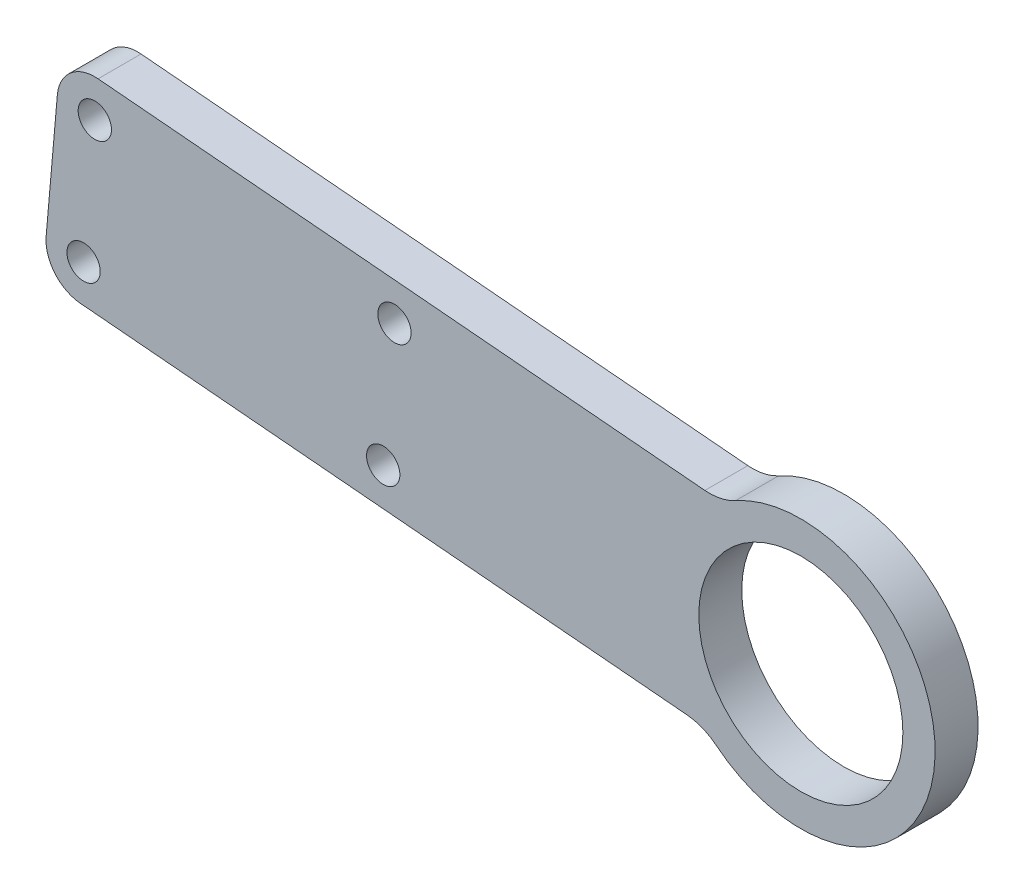
SolidWorks part; units mm, degrees
ref_plane "前视基准面" through (0, 0, 0) normal (0, 0, 1) x (1, 0, 0)
ref_plane "上视基准面" through (0, 0, 0) normal (0, 1, 0) x (1, 0, 0)
ref_plane "右视基准面" through (0, 0, 0) normal (1, 0, 0) x (0, 0, -1)
sketch "草图1" plane through (0, 0, 0) normal (0, 0, 1) x (1, 0, 0)
  line L0 (0, 0) -> (160, 0) construction
  line L1 (-8.9271, 3.2492) -> (-1.4962, 23.6654)
  line L2 (-1.4962, 23.6654) -> (160.828, 9.4638)
  line L3 (8.9271, -3.2492) -> (11.3716, 3.467)
  line L4 (11.3716, 3.467) -> (159.172, -9.4638)
  circle A0 centre (0, 0) radius 6
  arc A1 (-8.9271, 3.2492) -> (8.9271, -3.2492) centre (0, 0) ccw
  arc A2 (159.172, -9.4638) -> (160.828, 9.4638) centre (160, 0) ccw
  circle A3 centre (160, 0) radius 6
  dimension "D1" = 12
  dimension "D2" = 19
  dimension "D3" = 160
  dimension "D4" = 70
  dimension "D5" = 5
extrude "凸台-拉伸1" add sketch "草图1" along normal mid plane 4
sketch "草图2" plane through (0, 0, 2) normal (0, 0, 1) x (1, 0, 0)
  line L0 (8.9271, -3.2492) -> (11.3716, 3.467) construction
  line L1 (160.828, 9.4638) -> (-1.4962, 23.6654) construction
  line L2 (-1.4962, 23.6654) -> (-8.9271, 3.2492) construction
  line L3 (11.3716, 3.467) -> (159.172, -9.4638) construction
  circle A0 centre (0.8742, 19.9446) radius 1.55
  circle A1 centre (16.2206, 6.5562) radius 1.55
  circle A2 centre (11.9354, 3.2618) radius 0.6
  dimension "D1" = 3.5
  dimension "D2" = 3.5
  dimension "D3" = 3.5
  dimension "D4" = 3.5
  dimension "D5" = 3.1
  dimension "D6" = 1.2
extrude "切除-拉伸1" cut sketch "草图2" against normal through all
fillet "圆角1" radius 3.5 1 edges at (-1.4962, 23.6654, 0)
sketch "草图3" plane through (0, 0, 2) normal (0, 0, 1) x (1, 0, 0)
  line L0 (91.0944, 15.5648) -> (89.4384, -3.3629)
  line L1 (160.828, 9.4638) -> (1.1792, 23.4313) construction
  line L2 (12.5263, 3.366) -> (159.172, -9.4638) construction
  line L3 (89.4384, -3.3629) -> (159.172, -9.4638)
  line L4 (160.828, 9.4638) -> (91.0944, 15.5648)
  arc A0 (159.172, -9.4638) -> (160.828, 9.4638) centre (160, 0) ccw
  dimension "D1" = 70
extrude "切除-拉伸2" cut sketch "草图3" against normal through all flip side to cut
sketch "草图4" plane through (0, 0, 2) normal (0, 0, 1) x (1, 0, 0)
  line L0 (94.276, 11.773) -> (93.2301, -0.1813) construction
  line L1 (122.1694, 9.3327) -> (121.1236, -2.6217) construction
  line L2 (91.0944, 15.5648) -> (89.4384, -3.3629) construction
  line L3 (160.828, 9.4638) -> (91.0944, 15.5648) construction
  line L4 (89.4384, -3.3629) -> (159.172, -9.4638) construction
  line L5 (125.9612, 12.5143) -> (124.3052, -6.4134) construction
  circle A0 centre (94.276, 11.773) radius 1.55
  circle A1 centre (93.2301, -0.1813) radius 1.55
  circle A2 centre (122.1694, 9.3327) radius 1.55
  circle A3 centre (121.1236, -2.6217) radius 1.55
  circle A4 centre (160, 0) radius 6 construction
  dimension "D1" = 3.1
  dimension "D2" = 3.5
  dimension "D3" = 3.5
  dimension "D4" = 3.5
  dimension "D5" = 3.5
  dimension "D6" = 3.5
  dimension "D7" = 35
  dimension "D8" = 3.5
extrude "切除-拉伸3" cut sketch "草图4" against normal through all
fillet "圆角2" radius 3.5 2 edges at (89.4384, -3.3629, 0) (91.0944, 15.5648, 0)
sketch "草图5" plane through (0, 0, 2) normal (0, 0, 1) x (1, 0, 0)
  circle A0 centre (160, 0) radius 12.5
  dimension "D1" = 25
extrude "凸台-拉伸2" add sketch "草图5" against normal blind 4
sketch "草图6" plane through (0, 0, 2) normal (0, 0, 1) x (1, 0, 0)
  circle A0 centre (160, 0) radius 9.5
  dimension "D1" = 19
extrude "切除-拉伸4" cut sketch "草图6" against normal through all
fillet "圆角3" radius 5 2 edges at (152.7349, 10.1719, 0) (151.0789, -8.7558, 0)
